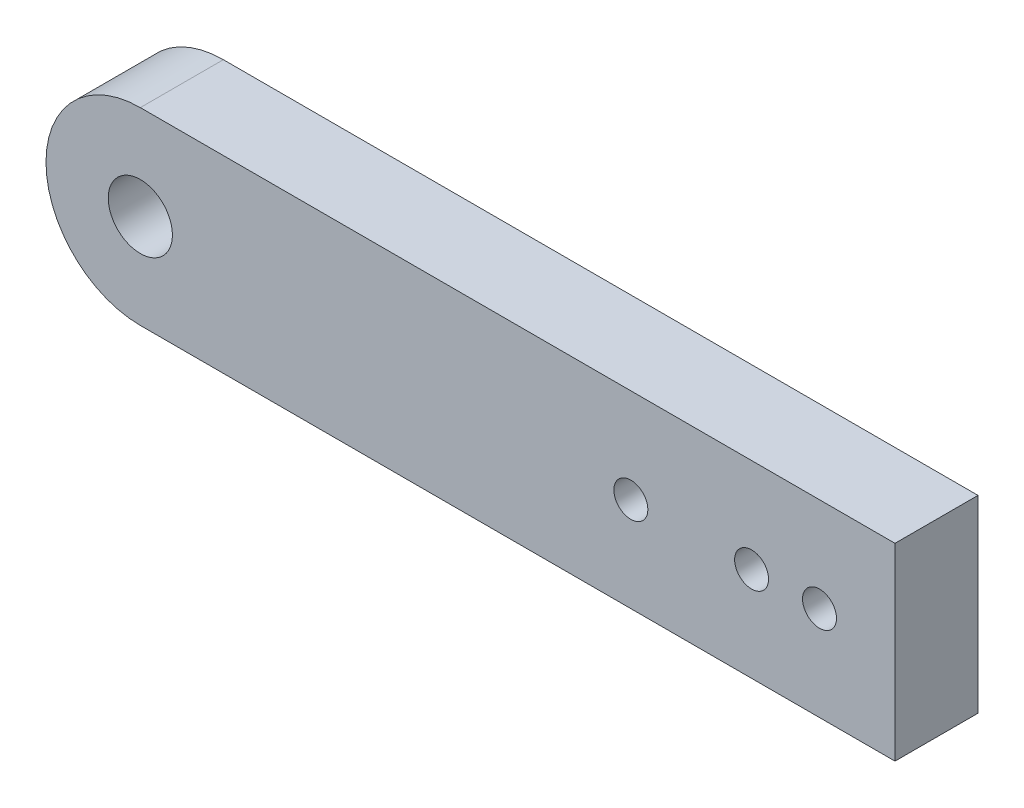
SolidWorks part; units mm, degrees
ref_plane "前视基准面" through (0, 0, 0) normal (0, 0, 1) x (1, 0, 0)
ref_plane "上视基准面" through (0, 0, 0) normal (0, 1, 0) x (1, 0, 0)
ref_plane "右视基准面" through (0, 0, 0) normal (1, 0, 0) x (0, 0, -1)
sketch "草图1" plane through (0, 0, 0) normal (0, 0, 1) x (1, 0, 0)
  line L0 (-61.0469, -2.5387) -> (71.8118, -2.5387) construction
  line L1 (-56.8283, 9.9613) -> (43.1717, 9.9613)
  line L3 (-56.8283, -15.0387) -> (43.1717, -15.0387)
  line L4 (43.1717, 9.9613) -> (43.1717, -15.0387)
  arc A0 (-56.8283, 9.9613) -> (-56.8283, -15.0387) centre (-56.8283, -2.5387) ccw
  circle A1 centre (33.1717, -2.5387) radius 2.25
  circle A2 centre (24.1717, -2.5387) radius 2.25
  circle A3 centre (8.1717, -2.5387) radius 2.25
  circle A4 centre (-56.8283, -2.5387) radius 4.25
  dimension "D1" = 4.5
  dimension "D2" = 9
  dimension "D3" = 25
  dimension "D6" = 8.5
  dimension "D7" = 10
  dimension "D4" = 90
  dimension "D5" = 25
extrude "凸台-拉伸1" add sketch "草图1" along normal blind 11
